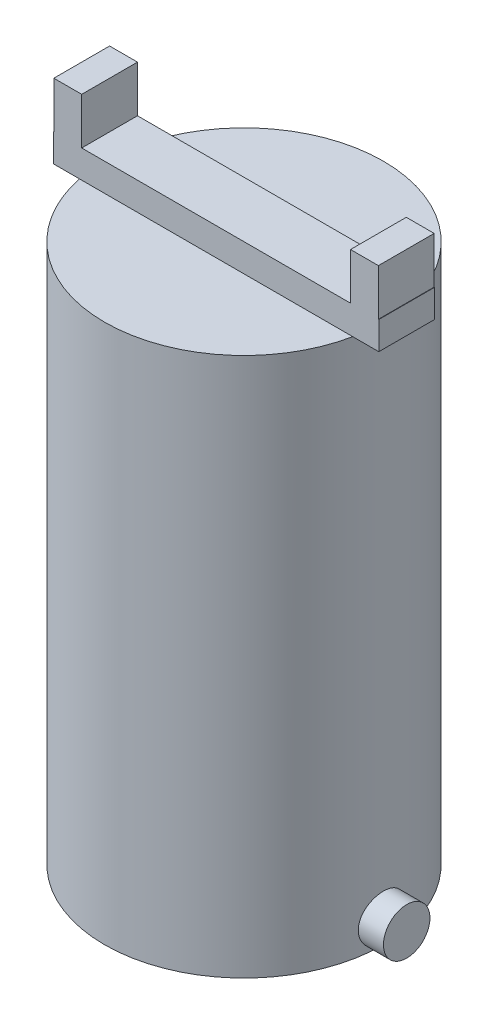
SolidWorks part; units mm, degrees
ref_plane "Front Plane" through (0, 0, 0) normal (0, 0, 1) x (1, 0, 0)
ref_plane "Top Plane" through (0, 0, 0) normal (0, 1, 0) x (1, 0, 0)
ref_plane "Right Plane" through (0, 0, 0) normal (1, 0, 0) x (0, 0, -1)
sketch "Sketch1" plane through (0, 0, 0) normal (0, 1, 0) x (1, 0, 0)
  circle A0 centre (0, 0) radius 15
  dimension "D1" = 30
extrude "Boss-Extrude1" add sketch "Sketch1" along normal blind 58
sketch "Sketch3" plane through (0, 0, 0) normal (1, 0, 0) x (0, 0, -1)
  circle A0 centre (0, 2.5) radius 2.5
  dimension "D2" = 5
  dimension "D1" = 2.5
sketch "Sketch4" plane through (0, 58, 0) normal (0, 1, 0) x (1, 0, 0)
  line L1 (-17.5, 3) -> (17.5, 3)
  line L2 (-17.5, 3) -> (-17.5, -3)
  line L3 (-17.5, -3) -> (17.5, -3)
  line L4 (17.5, 3) -> (17.5, -3)
  line L5 (-17.5, 3) -> (17.5, -3) construction
  line L6 (-17.5, -3) -> (17.5, 3) construction
  point P0 (0, 0)
  dimension "D1" = 6
  dimension "D2" = 35
extrude "Boss-Extrude3" add sketch "Sketch4" along normal blind 3
sketch "Sketch5" plane through (0, 61, 0) normal (0, 1, 0) x (1, 0, 0)
  line L0 (-17.5, -3) -> (17.5, -3) construction
  line L1 (-17.4575, 3) -> (-14.4575, 3)
  line L2 (-17.4575, 3) -> (-17.4575, -3)
  line L3 (-17.4575, -3) -> (-14.4575, -3)
  line L4 (-14.4575, 3) -> (-14.4575, -3)
  line L5 (-17.4575, 3) -> (-14.4575, -3) construction
  line L6 (-17.4575, -3) -> (-14.4575, 3) construction
  point P0 (-15.9575, 0)
  dimension "D1" = 3
extrude "Boss-Extrude4" add sketch "Sketch5" along normal blind 5
mirror "Mirror2" about plane through (0, 0, 0) normal (1, 0, 0) of "Boss-Extrude4"
sketch "Sketch6" plane through (0, 0, 0) normal (1, 0, 0) x (0, 0, -1)
  circle A0 centre (0, 2.5) radius 2.5
  dimension "D1" = 2.5
extrude "Boss-Extrude5" add sketch "Sketch6" along normal blind 17.5
mirror "Mirror3" about plane through (0, 0, 0) normal (1, 0, 0) of "Boss-Extrude5"
